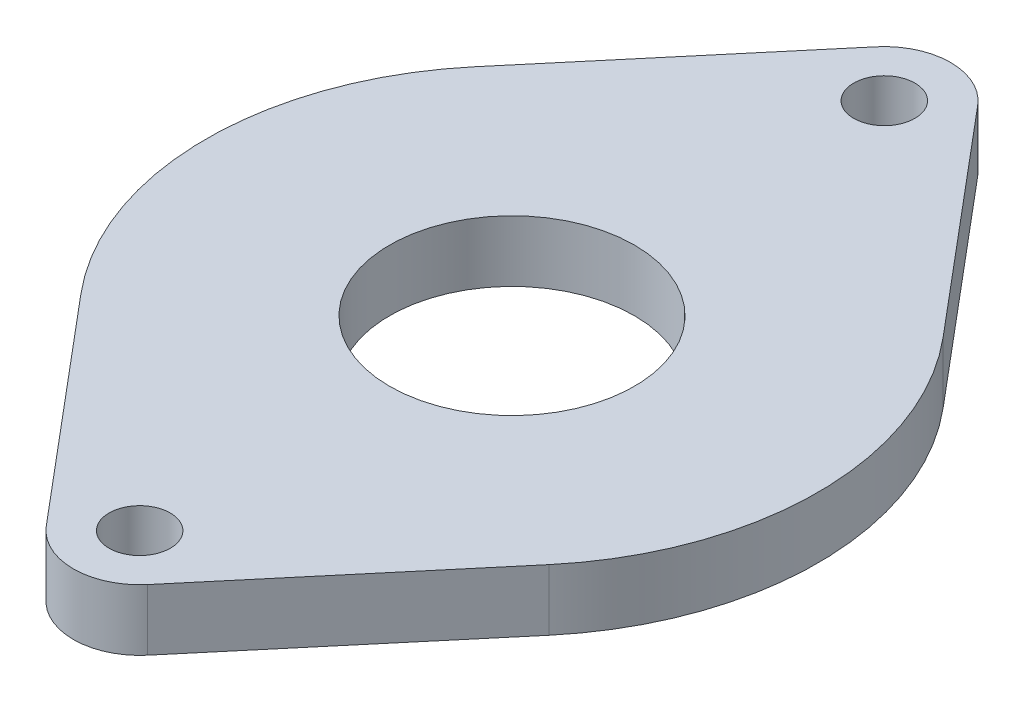
SolidWorks part; units mm, degrees
material "PEI"
ref_plane "Front Plane" through (0, 0, 0) normal (0, 0, 1) x (1, 0, 0)
ref_plane "Top Plane" through (0, 0, 0) normal (0, 1, 0) x (1, 0, 0)
ref_plane "Right Plane" through (0, 0, 0) normal (1, 0, 0) x (0, 0, -1)
sketch "Sketch1" plane through (0, 0, 0) normal (0, 1, 0) x (1, 0, 0)
  line L0 (0, -18.25) -> (0, 18.25)
  line L1 (2.4868, 20.3425) -> (11.4775, 9.6575)
  line L2 (-2.4868, 20.3425) -> (-11.4775, 9.6575)
  line L3 (0, 0) -> (15, 0)
  line L4 (-2.4868, -20.3425) -> (-11.4775, -9.6575)
  line L5 (2.4868, -20.3425) -> (11.4775, -9.6575)
  circle A0 centre (0, 0) radius 6
  circle A1 centre (0, 0) radius 15
  circle A2 centre (0, 18.25) radius 1.5
  circle A3 centre (0, 18.25) radius 3.25
  circle A4 centre (0, -18.25) radius 3.25
  circle A5 centre (0, -18.25) radius 1.5
  dimension "D1" = 12
  dimension "D2" = 30
  dimension "D4" = 3
  dimension "D3" = 18.25
extrude "Boss-Extrude1" add sketch "Sketch1" along normal blind 3
